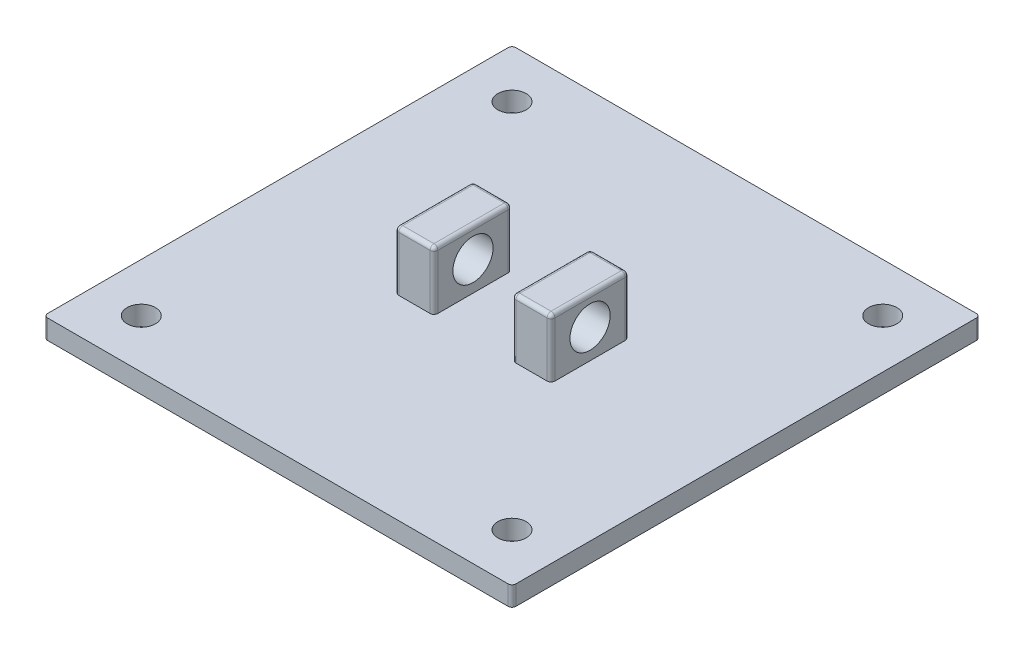
SolidWorks part; units mm, degrees
ref_plane "Plan de face" through (0, 0, 0) normal (0, 0, 1) x (1, 0, 0)
ref_plane "Plan de dessus" through (0, 0, 0) normal (0, 1, 0) x (1, 0, 0)
ref_plane "Plan de droite" through (0, 0, 0) normal (1, 0, 0) x (0, 0, -1)
sketch "Esquisse1" plane through (0, 0, 0) normal (0, 1, 0) x (1, 0, 0)
  line L1 (120, -120) -> (-120, -120)
  line L2 (120, -120) -> (120, 120)
  line L3 (120, 120) -> (-120, 120)
  line L4 (-120, -120) -> (-120, 120)
  line L5 (120, -120) -> (-120, 120) construction
  line L6 (120, 120) -> (-120, -120) construction
  point P0 (0, 0)
  dimension "D1" = 240
  dimension "D2" = 240
extrude "Boss.-Extru.1" add sketch "Esquisse1" along normal blind 10
sketch "Esquisse2" plane through (0, 10, 0) normal (0, 1, 0) x (1, 0, 0)
  line L0 (-1108.8186, -95) -> (48891.1814, -95) construction
  line L2 (-1033.3713, 95) -> (48966.6287, 95) construction
  line L4 (-95, -1034.6284) -> (-95, 48965.3716) construction
  line L6 (-120, -120) -> (120, -120) construction
  line L8 (120, 120) -> (-120, 120) construction
  line L9 (-120, 120) -> (-120, -120) construction
  line L10 (95, -1027.6838) -> (95, 48972.3162) construction
  line L11 (120, -120) -> (120, 120) construction
  circle A0 centre (-95, -95) radius 7.25
  circle A1 centre (-95, 95) radius 7.25
  circle A2 centre (95, 95) radius 7.25
  circle A3 centre (95, -95) radius 7.25
  dimension "D5" = 14.5
  dimension "D6" = 14.5
  dimension "D7" = 14.5
  dimension "D8" = 14.5
  dimension "D1" = 25
  dimension "D2" = 25
  dimension "D3" = 25
  dimension "D4" = 25
extrude "Enlèv. mat.-Extru.1" cut sketch "Esquisse2" against normal blind 10
sketch "Esquisse4" plane through (0, 10, 0) normal (0, 1, 0) x (1, 0, 0)
  line L0 (0, -912.775) -> (0, 49087.225) construction
  line L1 (-120, 120) -> (-120, -120) construction
  line L2 (-1031.7458, 0) -> (48968.2542, 0) construction
  line L3 (120, 120) -> (-120, 120) construction
  dimension "D1" = 120
  dimension "D2" = 120
sketch "Esquisse5" plane through (0, 10, 0) normal (0, 1, 0) x (1, 0, 0)
  line L0 (-60, -947.023) -> (-60, 49052.977) construction
  line L1 (-120, 120) -> (-120, -120) construction
  line L2 (60, -971.4486) -> (60, 49028.5514) construction
  line L3 (120, -120) -> (120, 120) construction
  line L4 (-30, -908.4043) -> (-30, 49091.5957) construction
  line L5 (0, -200912.775) -> (0, 249087.225) construction
  line L6 (30, -974.4192) -> (30, 49025.5808) construction
  line L8 (-20, -20) -> (-40, -20)
  line L9 (-20, -20) -> (-20, 20)
  line L10 (-20, 20) -> (-40, 20)
  line L11 (-40, -20) -> (-40, 20)
  line L12 (-20, -20) -> (-40, 20) construction
  line L13 (-20, 20) -> (-40, -20) construction
  line L14 (-201031.7458, 0) -> (248968.2542, 0) construction
  line L15 (40, 20) -> (20, 20)
  line L16 (40, 20) -> (40, -20)
  line L17 (40, -20) -> (20, -20)
  line L18 (20, 20) -> (20, -20)
  line L19 (40, 20) -> (20, -20) construction
  line L20 (40, -20) -> (20, 20) construction
  point P13 (-30, 0)
  point P19 (30, 0)
  dimension "D1" = 60
  dimension "D2" = 60
  dimension "D3" = 30
  dimension "D4" = 30
  dimension "D5" = 40
  dimension "D6" = 20
  dimension "D7" = 40
  dimension "D8" = 20
extrude "Boss.-Extru.5" add sketch "Esquisse5" along normal blind 30
sketch "Esquisse7" plane through (-40, 0, 0) normal (-1, 0, 0) x (0, 0, 1)
  line L0 (0, -970.2618) -> (0, 49029.7382) construction
  line L1 (-20, 40) -> (-20, 10) construction
  line L2 (-1020.4902, 25) -> (48979.5098, 25) construction
  line L3 (-20, 40) -> (20, 40) construction
  circle A0 centre (0, 25) radius 10.3
  dimension "D3" = 20.6
  dimension "D1" = 20
  dimension "D2" = 15
extrude "Enlèv. mat.-Extru.2" cut sketch "Esquisse7" against normal blind 80
fillet "Congé1" radius 2 1 edges at (-120, 5, -120)
fillet "Congé2" radius 2 1 edges at (-120, 5, 120)
fillet "Congé3" radius 2 1 edges at (120, 5, 120)
fillet "Congé4" radius 2 1 edges at (120, 5, -120)
fillet "Congé5" radius 2 1 edges at (30, 40, -20)
fillet "Congé6" radius 2 1 edges at (30, 40, 20)
fillet "Congé7" radius 2 5 edges at (40, 24, 20) (40, 39.4142, 19.4142) (40, 24, -20) (40, 39.4142, -19.4142) (40, 40, 0)
fillet "Congé8" radius 2 1 edges at (-20, 40, 0)
fillet "Congé9" radius 2 3 edges at (-20, 24, 20) (-20.5858, 39.4142, 20) (-31, 40, 20)
fillet "Congé10" radius 2 3 edges at (-40, 24, 20) (-40, 39.4142, 19.4142) (-40, 40, -1)
fillet "Congé11" radius 2 5 edges at (-20, 24, -20) (-20.5858, 39.4142, -20) (-40, 24, -20) (-39.4142, 39.4142, -20) (-30, 40, -20)
fillet "Congé12" radius 2 5 edges at (20, 24, -20) (20, 39.4142, -19.4142) (20, 24, 20) (20, 39.4142, 19.4142) (20, 40, 0)
